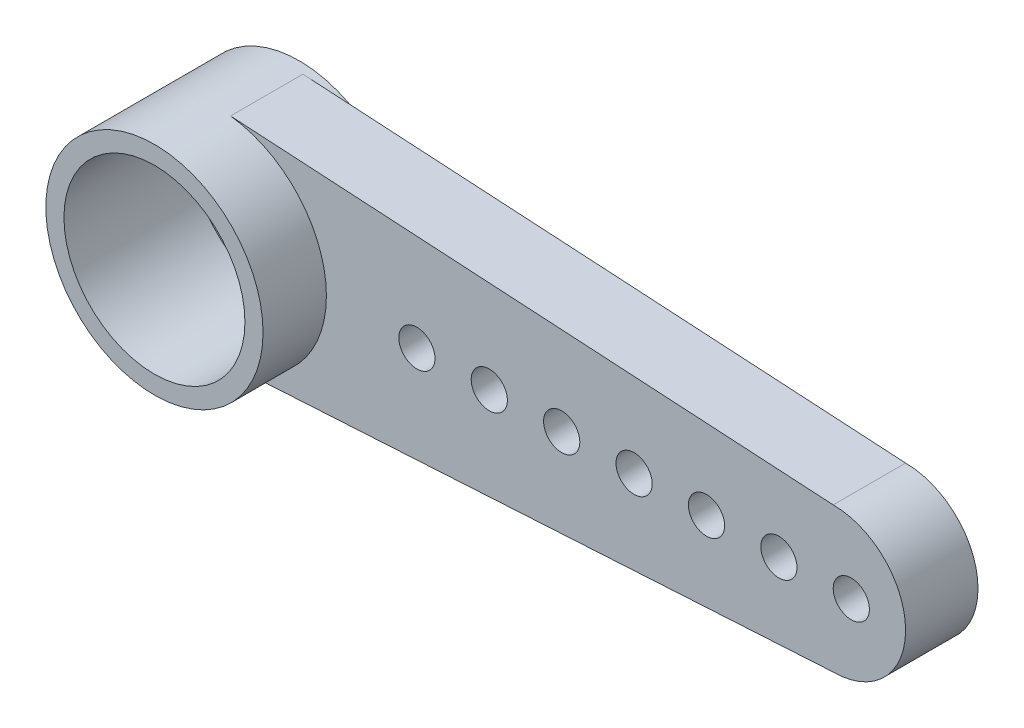
SolidWorks part; units mm, degrees
ref_plane "前视基准面" through (0, 0, 0) normal (0, 0, 1) x (1, 0, 0)
ref_plane "上视基准面" through (0, 0, 0) normal (0, 1, 0) x (1, 0, 0)
ref_plane "右视基准面" through (0, 0, 0) normal (1, 0, 0) x (0, 0, -1)
sketch "草图1" plane through (0, 0, 0) normal (0, 0, 1) x (1, 0, 0)
  circle A0 centre (0, 0) radius 3
  dimension "D1" = 6
extrude "凸台-拉伸1" add sketch "草图1" along normal blind 4
ref_plane "基准面1" through (0, 0, 0.25) normal (0, 0, -1) x (-1, 0, 0)
sketch "草图6" plane through (0, 0, 0.25) normal (0, 0, -1) x (-1, 0, 0)
  line L0 (3, 0) -> (3, 9.1111) construction
  line L1 (3, 9.1111) -> (-19, 9.1111) construction
  line L2 (-19, 9.1111) -> (-19, 0) construction
  line L3 (-19, 0) -> (3, 0) construction
  line L5 (0, 3) -> (0, -3) construction
  line L6 (-17, 2) -> (0, 3)
  line L7 (-17, -2) -> (0, -3)
  line L8 (0, 3) -> (0, -3)
  line L9 (-17.5, 0) -> (-15.5, 0) construction
  circle A0 centre (0, 0) radius 3 construction
  arc A1 (-17, 2) -> (-17, -2) centre (-17, 0) ccw
  circle A2 centre (-17.5, 0) radius 0.5
  circle A12 centre (-15.5, 0) radius 0.5
  circle A13 centre (-13.5, 0) radius 0.5
  circle A14 centre (-11.5, 0) radius 0.5
  circle A15 centre (-9.5, 0) radius 0.5
  circle A16 centre (-7.5, 0) radius 0.5
  circle A17 centre (-5.5, 0) radius 0.5
  dimension "D2" = 2
  dimension "D3" = 1
  dimension "D4" = 7
  dimension "D5" = 2
  dimension "D1" = 22
  dimension "D10" = 1.5
extrude "凸台-拉伸2" add sketch "草图6" against normal blind 2
sketch "草图3" plane through (0, 0, 0) normal (0, 0, -1) x (-1, 0, 0)
  circle A0 centre (0, 0) radius 2
  dimension "D1" = 4
extrude "切除-拉伸2" cut sketch "草图3" against normal blind 0.25
sketch "草图4" plane through (0, 0, 0.25) normal (0, 0, -1) x (-1, 0, 0)
  circle A0 centre (0, 0) radius 1.25
  dimension "D1" = 2.5
extrude "切除-拉伸3" cut sketch "草图4" against normal through all
sketch "草图2" plane through (0, 0, 4) normal (0, 0, 1) x (1, 0, 0)
  circle A0 centre (0, 0) radius 2.5
  dimension "D1" = 5
extrude "切除-拉伸1" cut sketch "草图2" against normal blind 3.5
